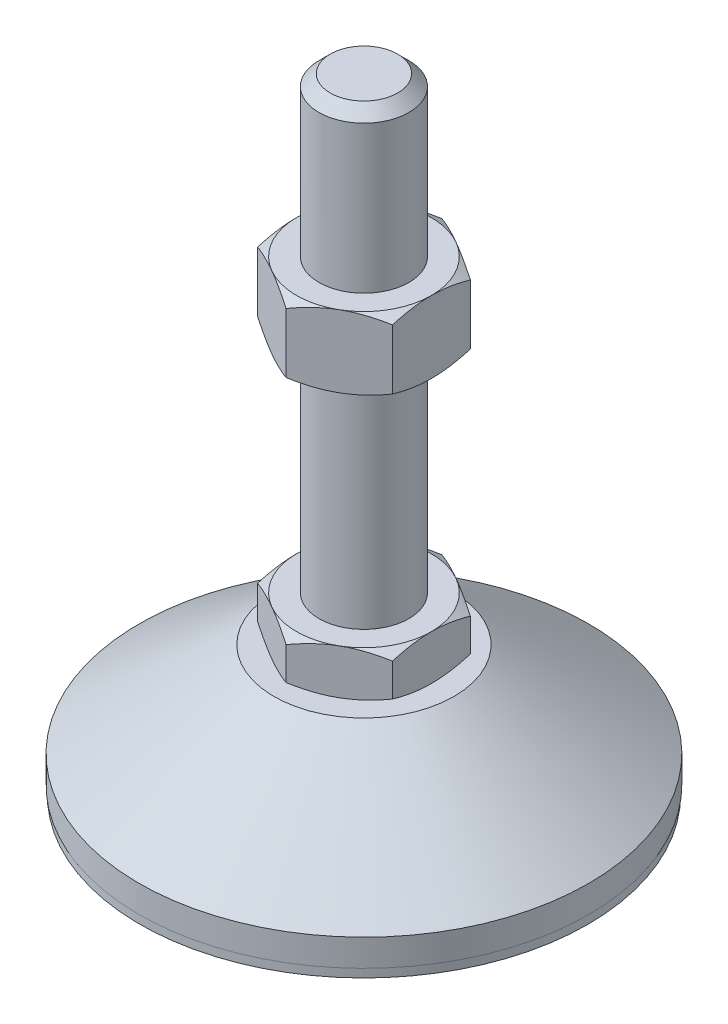
SolidWorks part; units mm, degrees
ref_plane "Спереди" through (0, 0, 0) normal (0, 0, 1) x (1, 0, 0)
ref_plane "Сверху" through (0, 0, 0) normal (0, 1, 0) x (1, 0, 0)
ref_plane "Справа" through (0, 0, 0) normal (1, 0, 0) x (0, 0, -1)
sketch "Эскиз1" plane through (0, 0, 0) normal (0, 0, 1) x (1, 0, 0)
  line L0 (0, 0) -> (-49.8, 0)
  line L1 (-49.8, 0) -> (-49.8, 2)
  line L2 (-49.8, 2) -> (-50, 2)
  line L3 (-50, 2) -> (-50, 8)
  line L4 (-50, 8) -> (-20, 29)
  line L5 (-20, 29) -> (-10, 29)
  line L12 (-10, 39) -> (-10, 136.5)
  line L13 (-10, 136.5) -> (-7.5, 139)
  line L14 (-7.5, 139) -> (0, 139)
  line L15 (0, 139) -> (0, 0) construction
  line L16 (-10, 29) -> (0, 29) construction
  line L17 (0, 0) -> (0, 139)
  line L18 (0, 0) -> (0, -7.9595) construction
  line L19 (-10, 39) -> (-10, 29)
  point P8 (-10, 87.75)
  point P23 (-15, 29)
  dimension "D1" = 20
  dimension "D2" = 29
  dimension "D3" = 10
  dimension "D4" = 100
  dimension "D5" = 10
  dimension "D6" = 2.5
  dimension "D7" = 45
  dimension "D8" = 40
  dimension "D9" = 2
  dimension "D10" = 100
  dimension "D11" = 6
  dimension "D12" = 0.2
revolve "Повернуть1" add sketch "Эскиз1" angle 360 about L17
sketch "Эскиз2" plane through (0, 29, 0) normal (0, 1, 0) x (1, 0, 0)
  line L1 (0, 17.3205) -> (-15, 8.6603)
  line L2 (-15, 8.6603) -> (-15, -8.6603)
  line L3 (-15, -8.6603) -> (0, -17.3205)
  line L4 (0, -17.3205) -> (15, -8.6603)
  line L5 (15, -8.6603) -> (15, 8.6603)
  line L6 (15, 8.6603) -> (0, 17.3205)
  circle A0 centre (0, 0) radius 15 construction
  dimension "D1" = 30
extrude "Бобышка-Вытянуть1" add sketch "Эскиз2" along normal up to vertex (10 mm away) up to point (-10, 39, 0)
ref_plane "Плоскость1" through (0, 87.75, 0) normal (0, 1, 0) x (1, 0, 0)
sketch "Эскиз3" plane through (0, 87.75, 0) normal (0, 1, 0) x (1, 0, 0)
  line L6 (15, 8.6603) -> (0, 17.3205)
  line L7 (0, 17.3205) -> (-15, 8.6603)
  line L8 (-15, 8.6603) -> (-15, -8.6603)
  line L9 (-15, -8.6603) -> (0, -17.3205)
  line L10 (0, -17.3205) -> (15, -8.6603)
  line L11 (15, -8.6603) -> (15, 8.6603)
  line L12 (15, 8.6603) -> (0, 17.3205)
  line L13 (0, 17.3205) -> (-15, 8.6603)
  line L14 (-15, 8.6603) -> (-15, -8.6603)
  line L15 (-15, -8.6603) -> (0, -17.3205)
  line L16 (0, -17.3205) -> (15, -8.6603)
  line L17 (15, -8.6603) -> (15, 8.6603)
  dimension "D1" = 0
extrude "Бобышка-Вытянуть2" add sketch "Эскиз3" along normal blind 16
sketch "Эскиз4" plane through (0, 0, 0) normal (0, 0, 1) x (1, 0, 0)
  line L0 (-15, 103.75) -> (-28.8564, 95.75)
  line L1 (-28.8564, 95.75) -> (-28.8564, 103.75)
  line L2 (-28.8564, 103.75) -> (-15, 103.75)
  line L3 (-28.8564, 95.75) -> (-15, 87.75)
  line L4 (50, 87.75) -> (-50, 87.75) construction
  line L5 (-15, 87.75) -> (-28.8564, 87.75)
  line L6 (-28.8564, 87.75) -> (-28.8564, 95.75)
  line L7 (-15, 103.75) -> (-15, 87.75) construction
  line L8 (-15, 39) -> (-23.6603, 39)
  line L9 (-23.6603, 39) -> (-23.6603, 34)
  line L10 (-23.6603, 34) -> (-15, 39)
  line L11 (-15, 29) -> (-23.6603, 34)
  line L12 (-23.6603, 34) -> (-23.6603, 29)
  line L13 (-23.6603, 29) -> (-15, 29)
  line L14 (0, 139) -> (0, 96.3793) construction
  dimension "D1" = 30
  dimension "D2" = 30
revolve "Вырез-Повернуть2" cut sketch "Эскиз4" angle 360 about L14
